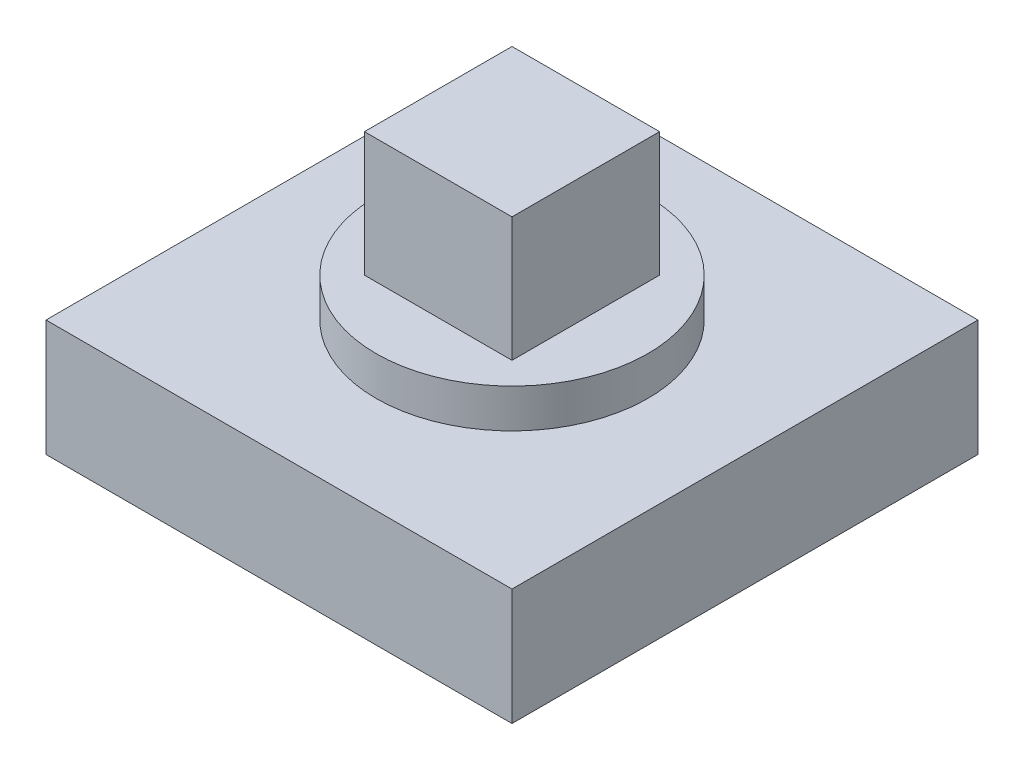
SolidWorks part; units mm, degrees
ref_plane "Front Plane" through (0, 0, 0) normal (0, 0, 1) x (1, 0, 0)
ref_plane "Top Plane" through (0, 0, 0) normal (0, 1, 0) x (1, 0, 0)
ref_plane "Right Plane" through (0, 0, 0) normal (1, 0, 0) x (0, 0, -1)
sketch "Sketch1" plane through (0, 0, 0) normal (0, 1, 0) x (1, 0, 0)
  line L1 (-6, -6) -> (6, -6)
  line L2 (-6, -6) -> (-6, 6)
  line L3 (-6, 6) -> (6, 6)
  line L4 (6, -6) -> (6, 6)
  point P8 (-1.3905, 8.6117)
  dimension "D1" = 12
  dimension "D2" = 6
  dimension "D3" = 6
extrude "Boss-Extrude1" add sketch "Sketch1" along normal blind 3
sketch "Sketch3" plane through (0, 3, 0) normal (0, 1, 0) x (1, 0, 0)
  circle A0 centre (0, 0) radius 3.5
  dimension "D1" = 7
extrude "Boss-Extrude2" add sketch "Sketch3" along normal blind 1
sketch "Sketch4" plane through (0, 4, 0) normal (0, 1, 0) x (1, 0, 0)
  line L1 (-1.9, 1.9) -> (1.9, 1.9)
  line L2 (-1.9, 1.9) -> (-1.9, -1.9)
  line L3 (-1.9, -1.9) -> (1.9, -1.9)
  line L4 (1.9, 1.9) -> (1.9, -1.9)
  dimension "D1" = 3.8
  dimension "D2" = 1.9
  dimension "D3" = 1.9
extrude "Boss-Extrude3" add sketch "Sketch4" along normal blind 3.2
